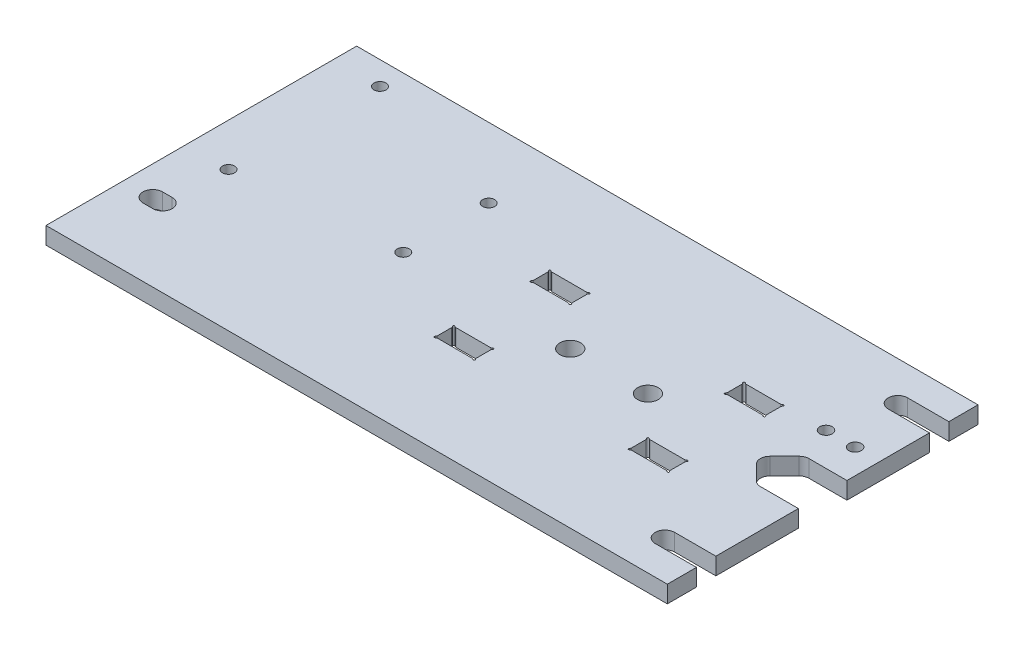
SolidWorks part; units mm, degrees
material "Acrylic (Medium-high impact)"
ref_plane "Front Plane" through (0, 0, 0) normal (0, 0, 1) x (1, 0, 0)
ref_plane "Top Plane" through (0, 0, 0) normal (0, 1, 0) x (1, 0, 0)
ref_plane "Right Plane" through (0, 0, 0) normal (1, 0, 0) x (0, 0, -1)
sketch "Sketch1" plane through (0, 0, 0) normal (0, 1, 0) x (1, 0, 0)
  line L0 (0, 11.3076) -> (0, -10.8315) construction
  line L1 (-101.6, 50.8) -> (101.6, 50.8)
  line L2 (-101.6, 50.8) -> (-101.6, -50.8)
  line L3 (-101.6, -50.8) -> (101.6, -50.8)
  line L4 (101.6, 50.8) -> (101.6, 7.9375)
  line L5 (-101.6, 50.8) -> (101.6, -50.8) construction
  line L6 (-101.6, -50.8) -> (101.6, 50.8) construction
  line L7 (-24.7577, 0) -> (22.1391, 0) construction
  line L8 (86.9273, 7.0076) -> (82.1648, 2.2451)
  line L9 (86.9273, -7.0076) -> (82.1648, -2.2451)
  line L10 (101.6, 0) -> (112.1126, 0) construction
  line L11 (101.6, -7.9375) -> (101.6, -50.8)
  line L12 (89.1724, 7.9375) -> (101.6, 7.9375)
  line L13 (89.1724, -7.9375) -> (101.6, -7.9375)
  circle A0 centre (-88.9, 38.1) radius 3.175 construction
  circle A1 centre (88.9, 38.1) radius 3.175 construction
  circle A2 centre (-88.9, -38.1) radius 3.175 construction
  circle A3 centre (88.9, -38.1) radius 3.175 construction
  circle A4 centre (88.9, 0) radius 3.175 construction
  circle A5 centre (88.9, 0) radius 6.35 construction
  arc A6 (82.1648, 2.2451) -> (82.1648, -2.2451) centre (84.4099, 0) ccw
  arc A7 (86.9273, -7.0076) -> (89.1724, -7.9375) centre (89.1724, -4.7625) ccw
  arc A8 (89.1724, 7.9375) -> (86.9273, 7.0076) centre (89.1724, 4.7625) ccw
  point P0 (0, 0)
  point P28 (79.9197, 0)
  point P33 (87.8572, -7.9375)
  point P36 (87.8572, 7.9375)
  dimension "D3" = 6.35
  dimension "D6" = 12.7
  dimension "D7" = 3.175
  dimension "D9" = 3.175
  dimension "D1" = 203.2
  dimension "D2" = 101.6
  dimension "D4" = 12.7
  dimension "D5" = 12.7
  dimension "D8" = 15.875
extrude "Boss-Extrude1" add sketch "Sketch1" along normal blind 5.588
hole_wizard "1/4 Clearance Hole1" positions "Sketch3" profile "Sketch2" hole size "1/4" standard "Ansi Inch" end condition up to next
sketch "Sketch3" plane through (0, 5.588, 0) normal (0, 1, 0) x (-1, 0, 0)
  line L0 (-101.6, -50.8) -> (101.6, -50.8) construction
  point P3 (-88.1062, 38.1)
  point P6 (-88.1062, -38.1)
  point P12 (88.9, 25.4)
  dimension "D1" = 76.2
  dimension "D2" = 0.7937
sketch "Sketch2" plane through (88.1062, 5.588, 38.1) normal (1, 0, 0) x (0, 0, 1)
  line L0 (0, 0) -> (0, 5.588)
  line L1 (0, 5.588) -> (3.175, 5.588)
  line L2 (3.175, 5.588) -> (3.175, 0)
  line L5 (3.175, 0) -> (0, 0)
  line L11 (0, -6.35) -> (0, 107.95) construction
  dimension "Thru Hole Dia." = 6.35
  dimension "Thru Hole Depth" = 5.588
sketch "Sketch4" plane through (0, 5.588, 0) normal (0, 1, 0) x (1, 0, 0)
  line L0 (88.1062, 41.275) -> (101.6, 41.275)
  line L1 (101.6, 7.9375) -> (101.6, 50.8) construction
  line L2 (88.1062, 34.925) -> (101.6, 34.925)
  line L3 (101.6, 34.925) -> (101.6, 41.275)
  circle A0 centre (88.1062, 38.1) radius 3.175 construction
  arc A1 (88.1062, 41.275) -> (88.1062, 34.925) centre (88.1062, 38.1) ccw
extrude "Cut-Extrude1" cut sketch "Sketch4" against normal up to next (5.588 mm away)
mirror "Mirror1" about plane through (0, 0, 0) normal (0, 0, 1) of "Cut-Extrude1"
sketch "Sketch5" plane through (0, 5.588, 0) normal (0, 1, 0) x (1, 0, 0)
  line L0 (-92.075, -25.4) -> (-88.9, -25.4) construction
  line L1 (-92.075, -22.225) -> (-88.9, -22.225)
  line L2 (-92.075, -28.575) -> (-88.9, -28.575)
  arc A0 (-92.075, -22.225) -> (-92.075, -28.575) centre (-92.075, -25.4) ccw
  arc A1 (-88.9, -28.575) -> (-88.9, -22.225) centre (-88.9, -25.4) ccw
  circle A3 centre (-88.9, -25.4) radius 3.175 construction
  point P3 (-90.4875, -25.4)
  dimension "D1" = 3.175
extrude "Cut-Extrude2" cut sketch "Sketch5" against normal up to next
sketch "Sketch6" plane through (0, 5.588, 0) normal (0, 1, 0) x (1, 0, 0)
  line L0 (-101.6, 45.72) -> (-101.6, -7.62)
  line L1 (-101.6, -7.62) -> (-33.02, -7.62)
  line L2 (-33.02, -7.62) -> (-33.02, 33.02)
  line L3 (-33.02, 33.02) -> (-35.56, 33.02)
  line L4 (-35.56, 33.02) -> (-35.56, 45.72)
  line L5 (-35.56, 45.72) -> (-101.6, 45.72)
  line L6 (-101.6, 50.8) -> (-101.6, -50.8) construction
  line L7 (101.6, 50.8) -> (-101.6, 50.8) construction
  point P0 (-86.36, 43.18)
  point P1 (-35.56, 27.94)
  point P2 (-35.56, 0)
  point P3 (-87.63, -5.08)
  dimension "D1" = 50.8
  dimension "D2" = 15.24
  dimension "D3" = 27.94
  dimension "D4" = 5.08
  dimension "D5" = 50.8
  dimension "D6" = 13.97
  dimension "D7" = 68.58
  dimension "D8" = 2.54
  dimension "D9" = 53.34
  dimension "D10" = 5.08
  dimension "D11" = 5.08
  dimension "D12" = 1.27
hole_wizard "#4 Clearance Hole1" positions "Sketch8" profile "Sketch7" hole size "#4" standard "Ansi Inch" end condition up to next
sketch "Sketch8" plane through (0, 5.588, 0) normal (0, 1, 0) x (-1, 0, 0)
  point P0 (86.36, -43.18)
  point P1 (35.56, -27.94)
  point P4 (35.56, 0)
  point P7 (87.63, 5.08)
sketch "Sketch7" plane through (-86.36, 5.588, -43.18) normal (1, 0, 0) x (0, 0, 1)
  line L0 (0, 0) -> (0, 5.588)
  line L1 (0, 5.588) -> (1.9685, 5.588)
  line L2 (1.9685, 5.588) -> (1.9685, 0)
  line L5 (1.9685, 0) -> (0, 0)
  line L11 (0, -6.35) -> (0, 107.95) construction
  dimension "Thru Hole Dia." = 3.937
  dimension "Thru Hole Depth" = 5.588
sketch "Sketch9" plane through (0, 5.588, 0) normal (0, 1, 0) x (1, 0, 0)
  line L0 (0, 0) -> (51.0478, 0) construction
  line L1 (31.75, 21.6464) -> (31.75, -6.4609) construction
  line L2 (-6.0325, 18.7198) -> (6.0325, 18.7198)
  line L3 (-6.35, 18.4023) -> (-6.35, 13.0175)
  line L4 (-6.0325, 12.7) -> (6.0325, 12.7)
  line L5 (6.35, 18.4023) -> (6.35, 13.0175)
  line L6 (-6.35, 18.7198) -> (6.35, 12.7) construction
  line L7 (-6.35, 12.7) -> (6.35, 18.7198) construction
  line L8 (69.85, 12.7) -> (57.15, 18.7198) construction
  line L9 (69.85, 18.7198) -> (57.15, 12.7) construction
  line L10 (57.15, 18.4023) -> (57.15, 13.0175)
  line L11 (69.5325, 12.7) -> (57.4675, 12.7)
  line L12 (69.85, 18.4023) -> (69.85, 13.0175)
  line L13 (69.5325, 18.7198) -> (57.4675, 18.7198)
  arc A0 (-6.0325, 18.7198) -> (-6.35, 18.4023) centre (-6.35, 18.7198) ccw
  arc A1 (6.35, 18.4023) -> (6.0325, 18.7198) centre (6.35, 18.7198) ccw
  arc A2 (6.0325, 12.7) -> (6.35, 13.0175) centre (6.35, 12.7) ccw
  arc A3 (-6.35, 13.0175) -> (-6.0325, 12.7) centre (-6.35, 12.7) ccw
  arc A4 (69.85, 13.0175) -> (69.5325, 12.7) centre (69.85, 12.7) cw
  arc A5 (57.4675, 12.7) -> (57.15, 13.0175) centre (57.15, 12.7) cw
  arc A6 (57.15, 18.4023) -> (57.4675, 18.7198) centre (57.15, 18.7198) cw
  arc A7 (69.5325, 18.7198) -> (69.85, 18.4023) centre (69.85, 18.7198) cw
  point P4 (0, 15.7099)
  point P30 (63.5, 15.7099)
  point P31 (31.75, 0)
  dimension "D6" = 0.635
  dimension "D1" = 50.8
  dimension "D2" = 25.4
  dimension "D3" = 12.7
  dimension "D4" = 6.0198
  dimension "D5" = 63.5
extrude "Cut-Extrude3" cut sketch "Sketch9" against normal up to next (5.588 mm away)
fillet "Fillet1" radius 0.635 16 edges at (69.5325, 2.794, -12.7) (69.85, 2.794, -13.0175) (69.85, 2.794, -18.4023) (69.5325, 2.794, -18.7198) (57.4675, 2.794, -12.7) (57.15, 2.794, -13.0175) (57.15, 2.794, -18.4023) (57.4675, 2.794, -18.7198) (6.35, 2.794, -13.0175) (6.0325, 2.794, -12.7) (6.35, 2.794, -18.4023) (6.0325, 2.794, -18.7198) (-6.0325, 2.794, -12.7) (-6.35, 2.794, -13.0175) (-6.35, 2.794, -18.4023) (-6.0325, 2.794, -18.7198)
mirror "Mirror2" about plane through (0, 0, 0) normal (0, 0, 1) of "Fillet1", "Cut-Extrude3"
hole_wizard "#10 Clearance Hole1" positions "Sketch11" profile "Sketch10" hole size "#10" standard "ANSI Inch" end condition up to next
sketch "Sketch11" plane through (0, 5.588, 0) normal (0, 1, 0) x (-1, 0, 0)
  line L1 (0, 0) -> (-51.0478, 0) construction
  line L2 (-44.45, 0) -> (-19.05, 0) construction
  line L3 (-5.64, 18.7198) -> (5.64, 18.7198) construction
  line L4 (-69.14, 18.7198) -> (-57.86, 18.7198) construction
  line L5 (-63.5, 18.7198) -> (0, 18.7198) construction
  line L7 (-31.75, 0) -> (-31.75, 18.7198) construction
  point P0 (-19.05, 0)
  point P37 (-44.45, 0)
  dimension "D1" = 25.4
sketch "Sketch10" plane through (19.05, 5.588, 0) normal (1, 0, 0) x (0, 0, 1)
  line L0 (0, 0) -> (0, 5.588)
  line L1 (0, 5.588) -> (3.3909, 5.588)
  line L2 (3.3909, 5.588) -> (3.3909, 0)
  line L5 (3.3909, 0) -> (0, 0)
  line L11 (0, -6.35) -> (0, 107.95) construction
  dimension "Thru Hole Dia." = 6.7818
  dimension "Thru Hole Depth" = 5.588
hole_wizard "Tap Drill for #4 Helicoil1" positions "Sketch13" profile "Sketch12" hole size "#4-40" standard "ANSI Inch"
sketch "Sketch13" plane through (0, 5.588, 0) normal (0, 1, 0) x (1, 0, 0)
  line L0 (89.1724, 7.9375) -> (101.6, 7.9375) construction
  line L1 (101.6, 7.9375) -> (101.6, 34.925) construction
  point P0 (93.4847, 18.7325)
  point P2 (83.9597, 18.7325)
  dimension "D1" = 10.795
  dimension "D2" = 9.525
  dimension "D3" = 8.1153
sketch "Sketch12" plane through (93.4847, 5.588, -18.7325) normal (1, 0, 0) x (0, 0, 1)
  line L0 (0, 0) -> (0, 7.5709)
  line L1 (0, 7.5709) -> (2.032, 6.35)
  line L2 (2.032, 6.35) -> (2.032, 0)
  line L5 (2.032, 0) -> (0, 0)
  line L10 (0, 7.5709) -> (-2.032, 6.35) construction
  line L11 (0, -6.35) -> (0, 107.95) construction
  dimension "Hole Dia." = 4.064
  dimension "Hole Depth" = 6.35
  dimension "Drill Angle" = 118
